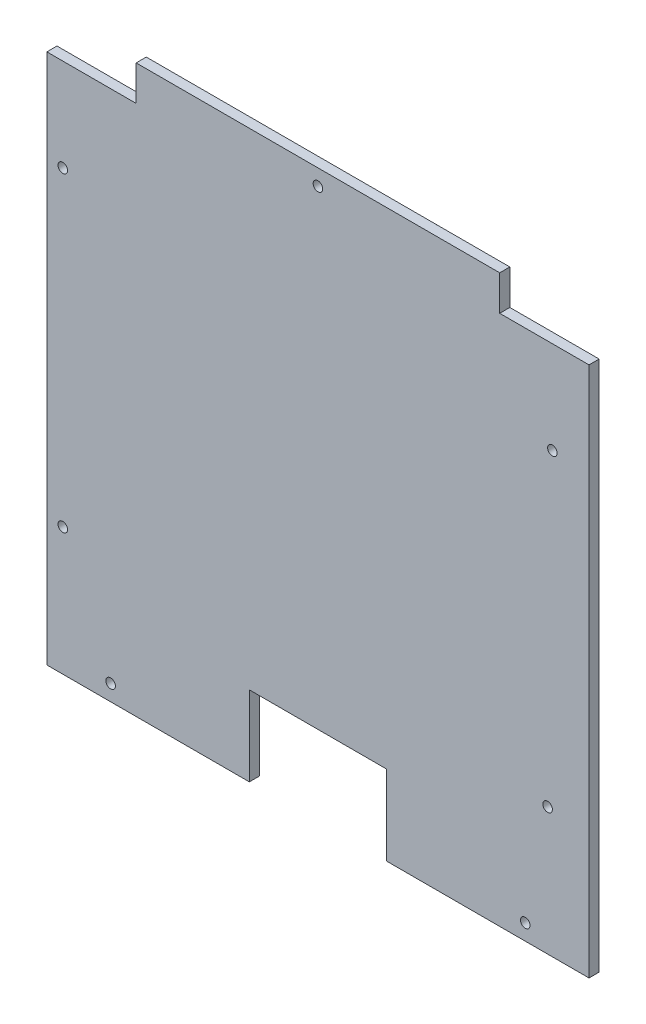
SolidWorks part; units mm, degrees
ref_plane "Front Plane" through (0, 0, 0) normal (0, 0, 1) x (1, 0, 0)
ref_plane "Top Plane" through (0, 0, 0) normal (0, 1, 0) x (1, 0, 0)
ref_plane "Right Plane" through (0, 0, 0) normal (1, 0, 0) x (0, 0, -1)
sketch "Sketch1" plane through (0, 0, 0) normal (0, 0, 1) x (1, 0, 0)
  line L1 (0, 0) -> (340, 0)
  line L2 (0, 0) -> (0, 355)
  line L3 (0, 355) -> (340, 355)
  line L4 (340, 0) -> (340, 355)
  line L7 (0, 333) -> (56, 333)
  line L8 (56, 355) -> (56, 333)
  line L11 (340, 333) -> (284, 333)
  line L12 (284, 355) -> (284, 333)
  line L14 (127, 0) -> (127, 50)
  line L15 (127, 50) -> (213, 50)
  line L16 (213, 0) -> (213, 50)
  circle A0 centre (40, 10) radius 3
  circle A1 centre (300, 10) radius 3
  circle A2 centre (170, 345) radius 3
  circle A3 centre (10, 275) radius 3
  circle A4 centre (10, 80) radius 3
  circle A5 centre (317.0233, 275) radius 3
  circle A6 centre (314.0233, 80) radius 3
  dimension "D9" = 6
  dimension "D10" = 6
  dimension "D11" = 6
  dimension "D12" = 6
  dimension "D13" = 6
  dimension "D14" = 6
  dimension "D15" = 6
  dimension "D16" = 10
  dimension "D1" = 355
  dimension "D2" = 340
  dimension "D3" = 22
  dimension "D4" = 56
  dimension "D5" = 56
  dimension "D6" = 50
  dimension "D7" = 86
  dimension "D8" = 127
  dimension "D17" = 10
  dimension "D18" = 10
  dimension "D19" = 10
  dimension "D20" = 10
  dimension "D21" = 40
  dimension "D22" = 40
  dimension "D23" = 80
  dimension "D24" = 80
  dimension "D25" = 80
  dimension "D26" = 80
  dimension "D27" = 170
extrude "Boss-Extrude1" add sketch "Sketch1" along normal blind 6.35 contours L16 L1 L4 L11 L12 L3 L8 L7 L2 L14 L15 A6 A5 A4 A3 A2 A1 A0
